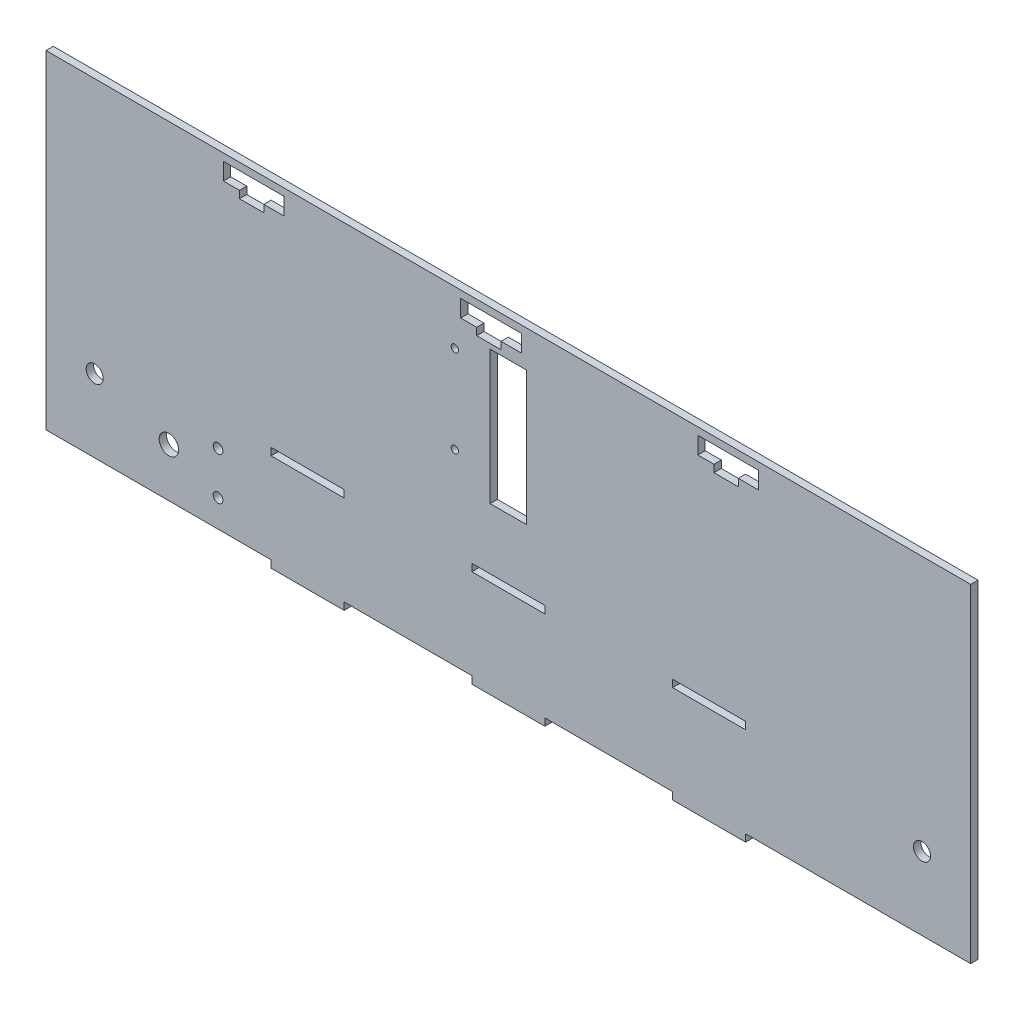
SolidWorks part; units mm, degrees
ref_plane "Alzado" through (0, 0, 0) normal (0, 0, 1) x (1, 0, 0)
ref_plane "Planta" through (0, 0, 0) normal (0, 1, 0) x (1, 0, 0)
ref_plane "Vista lateral" through (0, 0, 0) normal (1, 0, 0) x (0, 0, -1)
sketch "Croquis1" plane through (0, 0, 0) normal (0, 0, 1) x (1, 0, 0)
  line L0 (-190, -27.5) -> (190, -27.5) construction
  line L1 (-190, -67.5) -> (-97.5, -67.5)
  line L2 (-190, -67.5) -> (-190, 67.5)
  line L3 (-190, 67.5) -> (190, 67.5)
  line L4 (190, -67.5) -> (190, 67.5)
  line L5 (-190, -67.5) -> (190, 67.5) construction
  line L6 (-190, 67.5) -> (190, -67.5) construction
  line L7 (-190, 52.5) -> (190, 52.5) construction
  line L8 (67.5, -30.5) -> (97.5, -30.5)
  line L9 (-15, -30.5) -> (15, -30.5)
  line L10 (-15, -30.5) -> (-15, -27.5)
  line L11 (-15, -27.5) -> (15, -27.5)
  line L12 (15, -30.5) -> (15, -27.5)
  line L13 (-15, -30.5) -> (15, -27.5) construction
  line L14 (-15, -27.5) -> (15, -30.5) construction
  line L15 (67.5, -30.5) -> (67.5, -27.5)
  line L16 (67.5, -27.5) -> (97.5, -27.5)
  line L17 (97.5, -30.5) -> (97.5, -27.5)
  line L18 (67.5, -30.5) -> (97.5, -27.5) construction
  line L19 (67.5, -27.5) -> (97.5, -30.5) construction
  line L20 (-97.5, -30.5) -> (-67.5, -30.5)
  line L21 (-97.5, -30.5) -> (-97.5, -27.5)
  line L22 (-97.5, -27.5) -> (-67.5, -27.5)
  line L23 (-67.5, -30.5) -> (-67.5, -27.5)
  line L24 (-97.5, -30.5) -> (-67.5, -27.5) construction
  line L25 (-97.5, -27.5) -> (-67.5, -30.5) construction
  line L26 (0, 67.5) -> (0, -67.5) construction
  line L27 (-22, 67.5) -> (-22, -67.5) construction
  line L28 (-19.6, 64.5) -> (-19.6, 57.5)
  line L45 (-19.6, 57.5) -> (-13, 57.5)
  line L46 (-13, 57.5) -> (-13, 54.5)
  line L47 (-13, 54.5) -> (-3, 54.5)
  line L48 (-3, 54.5) -> (-3, 57.5)
  line L49 (-3, 57.5) -> (5.4, 57.5)
  line L50 (5.4, 57.5) -> (5.4, 64.5)
  line L51 (5.4, 64.5) -> (-19.6, 64.5)
  line L52 (0, 64.5) -> (0, 61) construction
  line L53 (-117.1, 64.5) -> (-117.1, 57.5)
  line L54 (-117.1, 57.5) -> (-110.5, 57.5)
  line L55 (-110.5, 57.5) -> (-110.5, 54.5)
  line L56 (-110.5, 54.5) -> (-100.5, 54.5)
  line L57 (-100.5, 54.5) -> (-100.5, 57.5)
  line L58 (-100.5, 57.5) -> (-92.1, 57.5)
  line L59 (-92.1, 57.5) -> (-92.1, 64.5)
  line L60 (-92.1, 64.5) -> (-117.1, 64.5)
  line L61 (-97.5, 64.5) -> (-97.5, 57.5) construction
  line L62 (77.9, 64.5) -> (77.9, 57.5)
  line L63 (77.9, 57.5) -> (84.5, 57.5)
  line L64 (84.5, 57.5) -> (84.5, 54.5)
  line L65 (84.5, 54.5) -> (94.5, 54.5)
  line L66 (94.5, 54.5) -> (94.5, 57.5)
  line L67 (94.5, 57.5) -> (102.9, 57.5)
  line L68 (102.9, 57.5) -> (102.9, 64.5)
  line L69 (102.9, 64.5) -> (77.9, 64.5)
  line L70 (97.5, 64.5) -> (97.5, 57.5) construction
  line L71 (-97.5, 67.5) -> (-97.5, 52.5) construction
  line L72 (97.5, 67.5) -> (97.5, 52.5) construction
  line L73 (-97.5, -70.5) -> (-67.5, -70.5)
  line L74 (-97.5, -70.5) -> (-97.5, -67.5)
  line L76 (-67.5, -70.5) -> (-67.5, -67.5)
  line L77 (-15, -70.5) -> (15, -70.5)
  line L78 (-15, -70.5) -> (-15, -67.5)
  line L80 (15, -70.5) -> (15, -67.5)
  line L81 (67.5, -70.5) -> (97.5, -70.5)
  line L82 (67.5, -70.5) -> (67.5, -67.5)
  line L84 (97.5, -70.5) -> (97.5, -67.5)
  line L85 (-67.5, -67.5) -> (-15, -67.5)
  line L86 (15, -67.5) -> (67.5, -67.5)
  line L87 (97.5, -67.5) -> (190, -67.5)
  line L89 (-7.5, 52.5) -> (7.5, 52.5)
  line L90 (-7.5, 52.5) -> (-7.5, -2.5)
  line L91 (-7.5, -2.5) -> (7.5, -2.5)
  line L92 (7.5, 52.5) -> (7.5, -2.5)
  circle A0 centre (-22, 45.5) radius 1.5
  circle A1 centre (-22, 9.5) radius 1.5
  circle A2 centre (-170, -37.5) radius 3.5
  circle A3 centre (-139.5, -47.5) radius 4
  circle A4 centre (-119.3, -38.75) radius 2
  circle A5 centre (-119.3, -56.25) radius 2
  circle A6 centre (170, -37.5) radius 3.5
  point P0 (0, 0)
  point P10 (0, -29)
  point P15 (82.5, -29)
  point P20 (-82.5, -29)
  dimension "D11" = 3
  dimension "D13" = 3
  dimension "D42" = 7
  dimension "D45" = 8
  dimension "D47" = 4
  dimension "D48" = 4
  dimension "D53" = 7
  dimension "D1" = 135
  dimension "400" = 380
  dimension "D2" = 40
  dimension "D3" = 15
  dimension "D4" = 3
  dimension "D5" = 30
  dimension "D6" = 3
  dimension "D7" = 3
  dimension "D8" = 82.5
  dimension "D9" = 82.5
  dimension "D10" = 22
  dimension "D12" = 7
  dimension "D14" = 37
  dimension "D15" = 3
  dimension "D16" = 25
  dimension "D17" = 7
  dimension "D18" = 10
  dimension "D19" = 3
  dimension "D20" = 19.6
  dimension "D21" = 25
  dimension "D22" = 7
  dimension "D23" = 10
  dimension "D24" = 3
  dimension "D25" = 19.6
  dimension "D26" = 25
  dimension "D27" = 7
  dimension "D28" = 10
  dimension "D29" = 3
  dimension "D30" = 19.6
  dimension "D31" = 3
  dimension "D32" = 92.5
  dimension "D33" = 3
  dimension "D34" = 92.5
  dimension "D35" = 3
  dimension "D36" = 3
  dimension "D37" = 3
  dimension "D38" = 3
  dimension "D39" = 15
  dimension "D40" = 55
  dimension "D41" = 7.5
  dimension "D43" = 20
  dimension "D44" = 30
  dimension "D46" = 50.5
  dimension "D49" = 17.5
  dimension "D50" = 11.25
  dimension "D51" = 70.7
  dimension "D52" = 20
  dimension "D54" = 20
  dimension "D55" = 30
extrude "Saliente-Extruir4" add sketch "Croquis1" along normal blind 3
